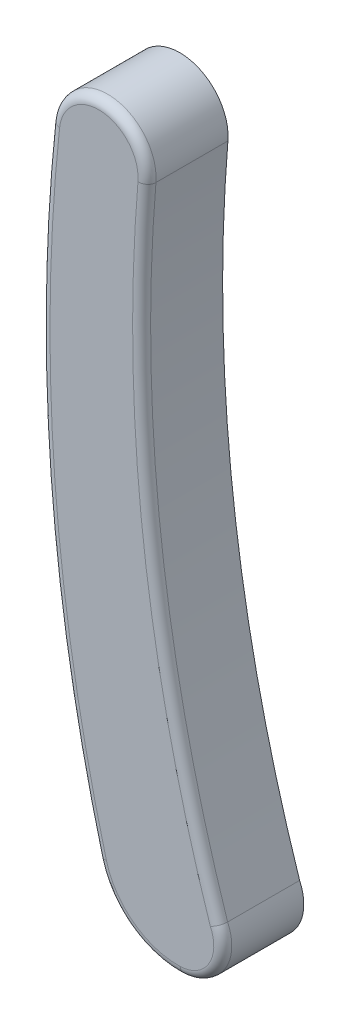
SolidWorks part; units mm, degrees
ref_plane "前视基准面" through (0, 0, 0) normal (0, 0, 1) x (1, 0, 0)
ref_plane "上视基准面" through (0, 0, 0) normal (0, 1, 0) x (1, 0, 0)
ref_plane "右视基准面" through (0, 0, 0) normal (1, 0, 0) x (0, 0, -1)
sketch "Sketch1" plane through (0, 0, 0) normal (0, 0, 1) x (1, 0, 0)
  arc A5 (0.8359, 17.0683) -> (-4.5132, 17.58) centre (-1.8416, 17.2927) ccw
  arc A6 (-4.5132, 17.58) -> (-1.8994, -16.5509) centre (88.713, 7.554) ccw
  arc A7 (-1.8994, -16.5509) -> (2.6994, -19.9776) centre (2.5608, -15.3644) ccw
  arc A8 (2.6994, -19.9776) -> (4.8193, -16.5206) centre (2.6266, -17.5545) ccw
  arc A9 (0.8359, 17.0683) -> (4.8193, -16.5206) centre (84.9763, 10.0159) ccw
extrude "Extrude1" add sketch "Sketch1" along normal blind 4.5
fillet "Fillet1" radius 0.5 5 edges at (4.6932, -18.8218, 4.5) (-0.1969, -19.0653, 4.5) (-4.7771, 0.3943, 4.5) (-1.5858, 19.9675, 4.5) (1.1285, 0.0723, 4.5)
